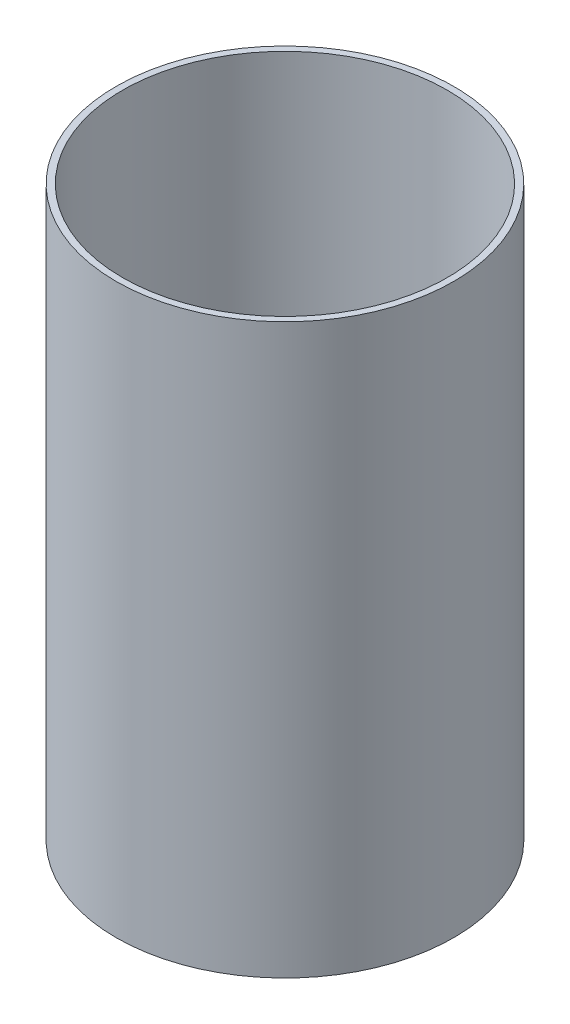
SolidWorks part; units mm, degrees
material "PTFE (general)"
ref_plane "Front Plane" through (0, 0, 0) normal (0, 0, 1) x (1, 0, 0)
ref_plane "Top Plane" through (0, 0, 0) normal (0, 1, 0) x (1, 0, 0)
ref_plane "Right Plane" through (0, 0, 0) normal (1, 0, 0) x (0, 0, -1)
ref_axis "Axis1" through (0, 55, 0) along (0, -1, 0)
sketch "Sketch2" plane through (0, 0, 0) normal (0, 0, 1) x (1, 0, 0)
  line L1 (-39.624, 0) -> (-38.1, 0)
  line L2 (-39.624, 0) -> (-39.624, -133.35)
  line L3 (-39.624, -133.35) -> (-38.1, -133.35)
  line L4 (-38.1, 0) -> (-38.1, -133.35)
  point P4 (0, 0)
  point P5 (0, 0)
  dimension "D2" = 1.524
revolve "Revolve1" add sketch "Sketch2" angle 360 about axis through (0, 55, 0) along (0, -1, 0)
equation "\"D2@Sketch2\"=\"LINER THICKNESS@Cryo Tank.Assembly\""
